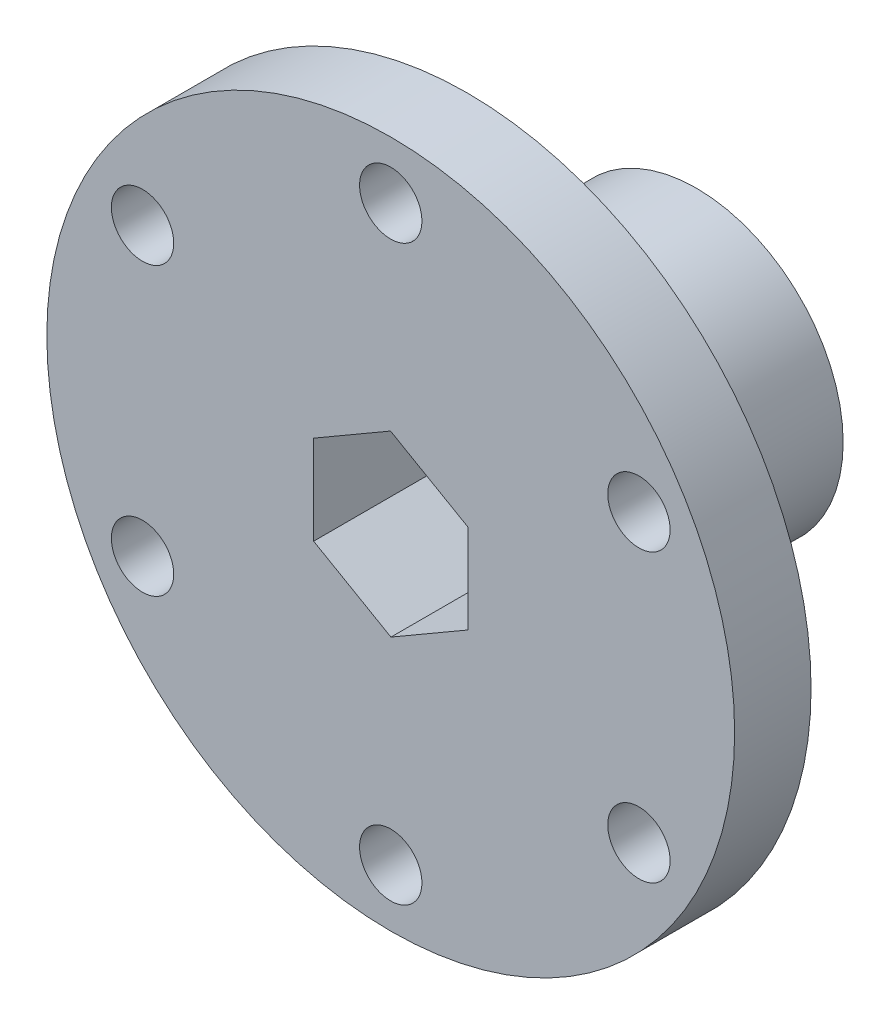
SolidWorks part; units mm, degrees
ref_plane "Front Plane" through (0, 0, 0) normal (0, 0, 1) x (1, 0, 0)
ref_plane "Top Plane" through (0, 0, 0) normal (0, 1, 0) x (1, 0, 0)
ref_plane "Right Plane" through (0, 0, 0) normal (1, 0, 0) x (0, 0, -1)
sketch "Sketch1" plane through (0, 0, 0) normal (0, 0, 1) x (1, 0, 0)
  circle A0 centre (0, 0) radius 28.575
  circle A1 centre (0, 0) radius 23.8125 construction
  circle A2 centre (0, 23.8125) radius 2.5908
  circle A3 centre (20.6222, 11.9063) radius 2.5908
  circle A4 centre (20.6222, -11.9062) radius 2.5908
  circle A5 centre (0, -23.8125) radius 2.5908
  circle A6 centre (-20.6222, -11.9063) radius 2.5908
  circle A7 centre (-20.6222, 11.9062) radius 2.5908
  point P19 (0, 0)
  dimension "D1" = 57.15
  dimension "D2" = 47.625
  dimension "D3" = 5.1816
  dimension "D4" = 6
extrude "Boss-Extrude1" add sketch "Sketch1" along normal blind 6.35
sketch "Sketch2" plane through (0, 0, 0) normal (0, 0, -1) x (-1, 0, 0)
  circle A0 centre (0, 0) radius 12.192
extrude "Boss-Extrude2" add sketch "Sketch2" along normal blind 19.05
sketch "Sketch3" plane through (0, 0, 6.35) normal (0, 0, 1) x (1, 0, 0)
  line L1 (6.4215, -3.689) -> (6.4055, 3.7167)
  line L2 (6.4055, 3.7167) -> (-0.016, 7.4057)
  line L3 (-0.016, 7.4057) -> (-6.4215, 3.689)
  line L4 (-6.4215, 3.689) -> (-6.4055, -3.7167)
  line L5 (-6.4055, -3.7167) -> (0.016, -7.4057)
  line L6 (0.016, -7.4057) -> (6.4215, -3.689)
  circle A0 centre (0, 0) radius 6.4135 construction
extrude "Cut-Extrude1" cut sketch "Sketch3" against normal through all
